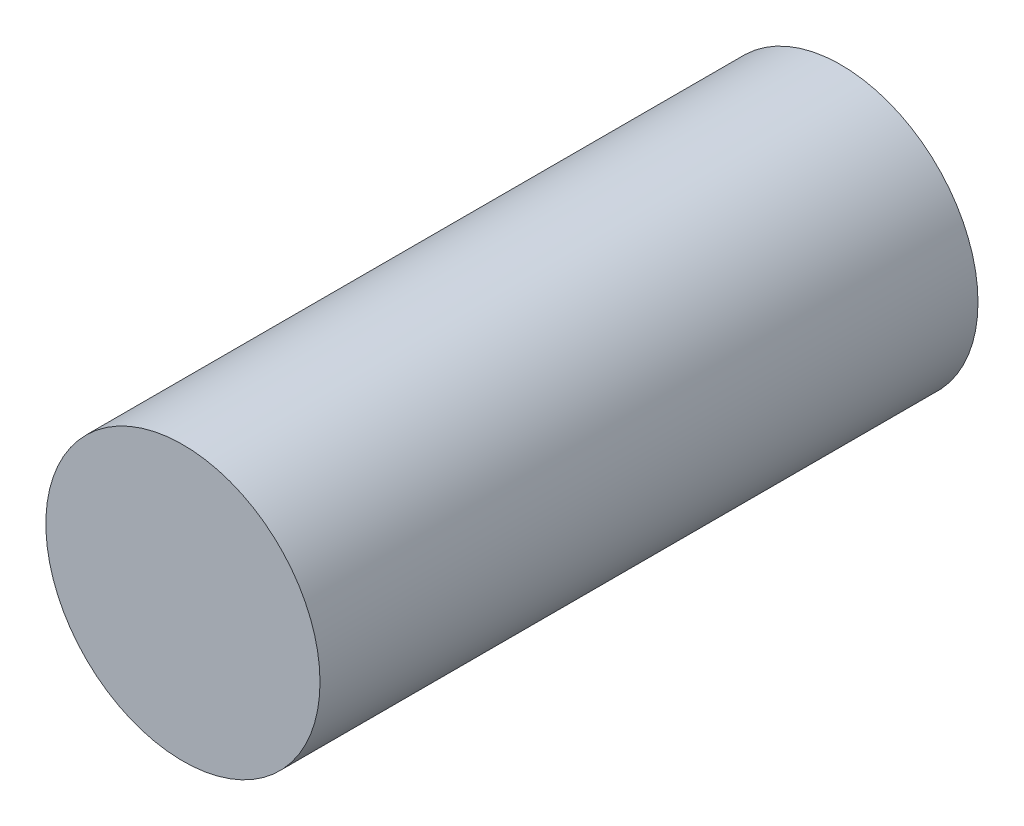
SolidWorks part; units mm, degrees
ref_plane "Front Plane" through (0, 0, 0) normal (0, 0, 1) x (1, 0, 0)
ref_plane "Top Plane" through (0, 0, 0) normal (0, 1, 0) x (1, 0, 0)
ref_plane "Right Plane" through (0, 0, 0) normal (1, 0, 0) x (0, 0, -1)
sketch "Sketch1" plane through (0, 0, 0) normal (0, 0, 1) x (1, 0, 0)
  circle A0 centre (0, 0) radius 1.25
  dimension "D1" = 2.5
extrude "Boss-Extrude1" add sketch "Sketch1" along normal blind 6
